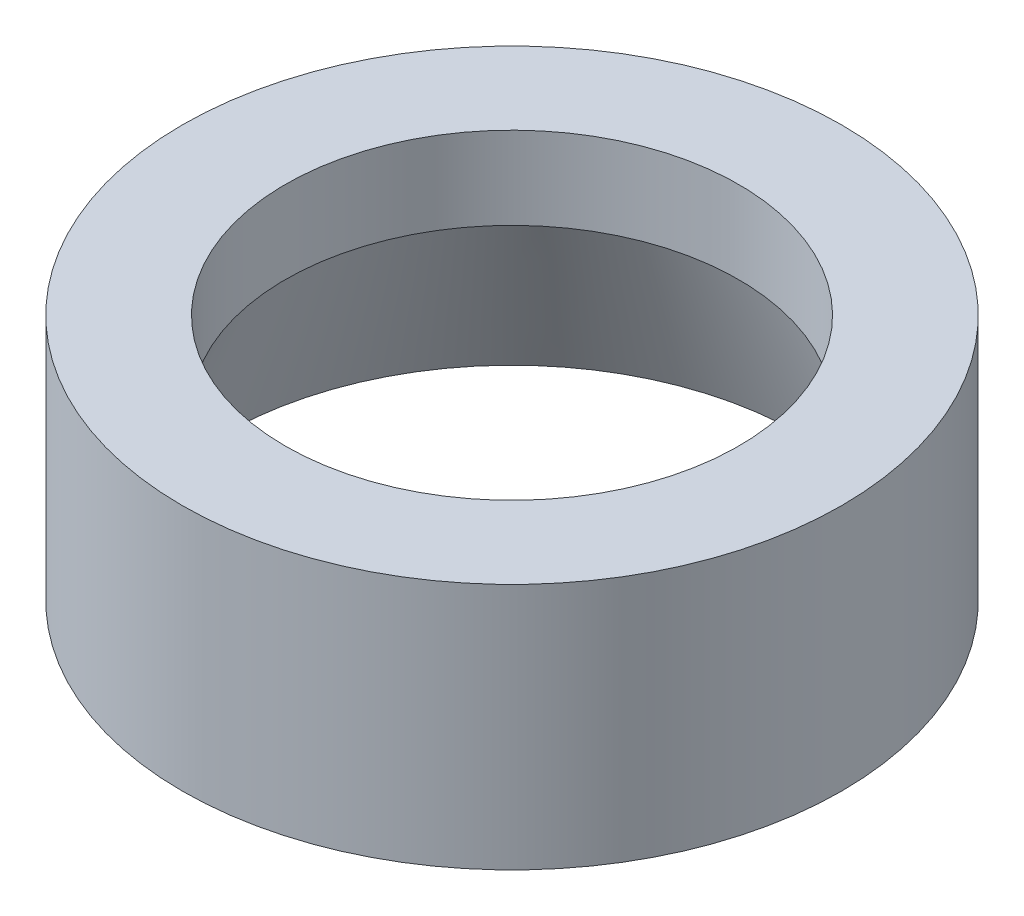
SolidWorks part; units mm, degrees
material "Brass"
ref_plane "Front Plane" through (0, 0, 0) normal (0, 0, 1) x (1, 0, 0)
ref_plane "Top Plane" through (0, 0, 0) normal (0, 1, 0) x (1, 0, 0)
ref_plane "Right Plane" through (0, 0, 0) normal (1, 0, 0) x (0, 0, -1)
sketch "Sketch1" plane through (0, 0, 0) normal (0, 0, 1) x (1, 0, 0)
  line L0 (0, 1.5) -> (0, -1.5) construction
  line L1 (4, 1.5) -> (4, -1.5)
  line L2 (4, -1.5) -> (3.5, -1.5)
  line L3 (3.5, -1.5) -> (2.75, 0.5)
  line L4 (2.75, 0.5) -> (2.75, 1.5)
  line L5 (2.75, 1.5) -> (4, 1.5)
  dimension "D1" = 3
  dimension "D2" = 8
  dimension "D3" = 5.5
  dimension "D4" = 1
  dimension "D5" = 0.5
revolve "Revolve1" add sketch "Sketch1" angle 360 about L0
